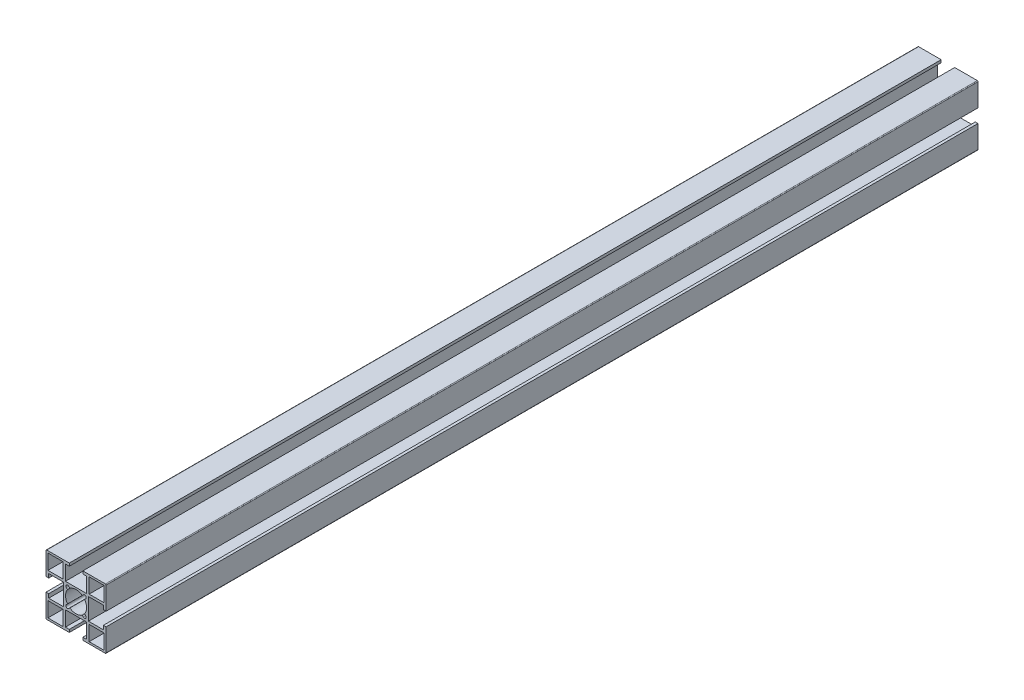
SolidWorks part; units mm, degrees
ref_plane "前视基准面" through (0, 0, 0) normal (0, 0, 1) x (1, 0, 0)
ref_plane "上视基准面" through (0, 0, 0) normal (0, 1, 0) x (1, 0, 0)
ref_plane "右视基准面" through (0, 0, 0) normal (1, 0, 0) x (0, 0, -1)
other "Configuration Table"
sketch "草图1" plane through (0, 0, 0) normal (1, 0, 0) x (0, 0, -1)
  line L0 (0, 0) -> (580, 0)
other "铝型材 40 X 40A X R0.5(1)"
ref_plane "基准面1" through (0, 0, 0) normal (0, 0, -1) x (0, 1, 0)
sketch "Sketch1" plane through (0, 0, 0) normal (0, 0, -1) x (0, 1, 0)
  line L0 (0, 0) -> (0, 16.3773) construction
  line L1 (0, 0) -> (-5.6569, 5.6569) construction
  line L2 (-19.5, 20) -> (-4.5, 20)
  line L3 (-20, 19.5) -> (-20, 4.5)
  line L4 (-19.5, -20) -> (-4.5, -20)
  line L5 (20, 19.5) -> (20, 4.5)
  line L6 (-4.879, 6.4347) -> (-4.1104, 5.6661)
  line L7 (-6.4347, 4.879) -> (-5.6661, 4.1104)
  line L8 (6.4347, 4.879) -> (5.6661, 4.1104)
  line L9 (0, 0) -> (20, 0) construction
  line L10 (4.879, 6.4347) -> (4.1104, 5.6661)
  line L11 (4.879, -6.4347) -> (4.1104, -5.6661)
  line L12 (6.4347, -4.879) -> (5.6661, -4.1104)
  line L13 (-6.4347, -4.879) -> (-5.6661, -4.1104)
  line L14 (-4.879, -6.4347) -> (-4.1104, -5.6661)
  line L15 (-4.5, 20) -> (-4.5, 18.2)
  line L16 (-18.7, 18.7) -> (-8.7, 18.7)
  line L17 (-18.7, 18.7) -> (-18.7, 8.7)
  line L18 (-18.7, 8.7) -> (-8.7, 8.7)
  line L19 (-8.7, 18.7) -> (-8.7, 8.7)
  line L20 (-7.1, 18.2) -> (-4.5, 18.2)
  line L21 (-7.1, 18.2) -> (-7.1, 8.2)
  line L22 (-7.1, 8.2) -> (7.1, 8.2)
  line L23 (7.1, 18.2) -> (7.1, 8.2)
  line L24 (4.5, 20) -> (4.5, 18.2)
  line L25 (4.5, 20) -> (19.5, 20)
  line L26 (4.5, 18.2) -> (7.1, 18.2)
  line L27 (8.7, 18.7) -> (8.7, 8.7)
  line L28 (18.7, 8.7) -> (8.7, 8.7)
  line L29 (18.7, 18.7) -> (18.7, 8.7)
  line L30 (18.7, 18.7) -> (8.7, 18.7)
  line L31 (18.2, 7.1) -> (8.2, 7.1)
  line L32 (18.2, 7.1) -> (18.2, 4.5)
  line L33 (20, 4.5) -> (18.2, 4.5)
  line L34 (8.2, 7.1) -> (8.2, -7.1)
  line L35 (18.2, -7.1) -> (8.2, -7.1)
  line L36 (18.2, -4.5) -> (18.2, -7.1)
  line L37 (20, -4.5) -> (18.2, -4.5)
  line L38 (7.1, -18.2) -> (7.1, -8.2)
  line L39 (7.1, -18.2) -> (4.5, -18.2)
  line L40 (4.5, -20) -> (4.5, -18.2)
  line L41 (7.1, -8.2) -> (-7.1, -8.2)
  line L42 (-7.1, -18.2) -> (-7.1, -8.2)
  line L43 (-4.5, -18.2) -> (-7.1, -18.2)
  line L44 (-4.5, -20) -> (-4.5, -18.2)
  line L45 (-18.2, -7.1) -> (-8.2, -7.1)
  line L46 (-18.2, -7.1) -> (-18.2, -4.5)
  line L47 (-20, -4.5) -> (-18.2, -4.5)
  line L48 (-8.2, -7.1) -> (-8.2, 7.1)
  line L49 (-18.2, 7.1) -> (-8.2, 7.1)
  line L50 (-18.2, 4.5) -> (-18.2, 7.1)
  line L51 (-20, 4.5) -> (-18.2, 4.5)
  line L52 (4.5, -20) -> (19.5, -20)
  line L53 (-20, -4.5) -> (-20, -19.5)
  line L54 (20, -4.5) -> (20, -19.5)
  line L55 (18.7, -18.7) -> (18.7, -8.7)
  line L56 (18.7, -8.7) -> (8.7, -8.7)
  line L57 (8.7, -18.7) -> (8.7, -8.7)
  line L58 (18.7, -18.7) -> (8.7, -18.7)
  line L59 (-8.7, -18.7) -> (-8.7, -8.7)
  line L60 (-18.7, -8.7) -> (-8.7, -8.7)
  line L61 (-18.7, -18.7) -> (-8.7, -18.7)
  line L62 (-18.7, -18.7) -> (-18.7, -8.7)
  arc A0 (-4.1104, 5.6661) -> (4.1104, 5.6661) centre (0, 0) cw
  arc A1 (-4.879, 6.4347) -> (-6.4347, 4.879) centre (-5.6569, 5.6569) ccw
  arc A2 (-4.1104, -5.6661) -> (4.1104, -5.6661) centre (0, 0) ccw
  arc A3 (-5.6661, 4.1104) -> (-5.6661, -4.1104) centre (0, 0) ccw
  arc A4 (6.4347, 4.879) -> (4.879, 6.4347) centre (5.6569, 5.6569) ccw
  arc A5 (4.879, -6.4347) -> (6.4347, -4.879) centre (5.6569, -5.6569) ccw
  arc A6 (-6.4347, -4.879) -> (-4.879, -6.4347) centre (-5.6569, -5.6569) ccw
  arc A7 (5.6661, 4.1104) -> (5.6661, -4.1104) centre (0, 0) cw
  arc A8 (-19.5, 20) -> (-20, 19.5) centre (-19.5, 19.5) ccw
  arc A9 (19.5, 20) -> (20, 19.5) centre (19.5, 19.5) cw
  arc A10 (19.5, -20) -> (20, -19.5) centre (19.5, -19.5) ccw
  arc A11 (-20, -19.5) -> (-19.5, -20) centre (-19.5, -19.5) ccw
  point P86 (20, 20)
  point P87 (-20, 20)
  point P88 (-20, -20)
  point P89 (20, -20)
  point P90 (0, 0)
  dimension "D2" = 7
  dimension "D3" = 45
  dimension "D4" = 1.1
  dimension "D5" = 1.8
  dimension "D6" = 8
  dimension "D7" = 1.3
  dimension "D8" = 14.2
  dimension "D10" = 10
  dimension "D11" = 10
  dimension "D12" = 40
  dimension "D13" = 9
  dimension "D14" = 0.5
  dimension "D9" = 1.3
